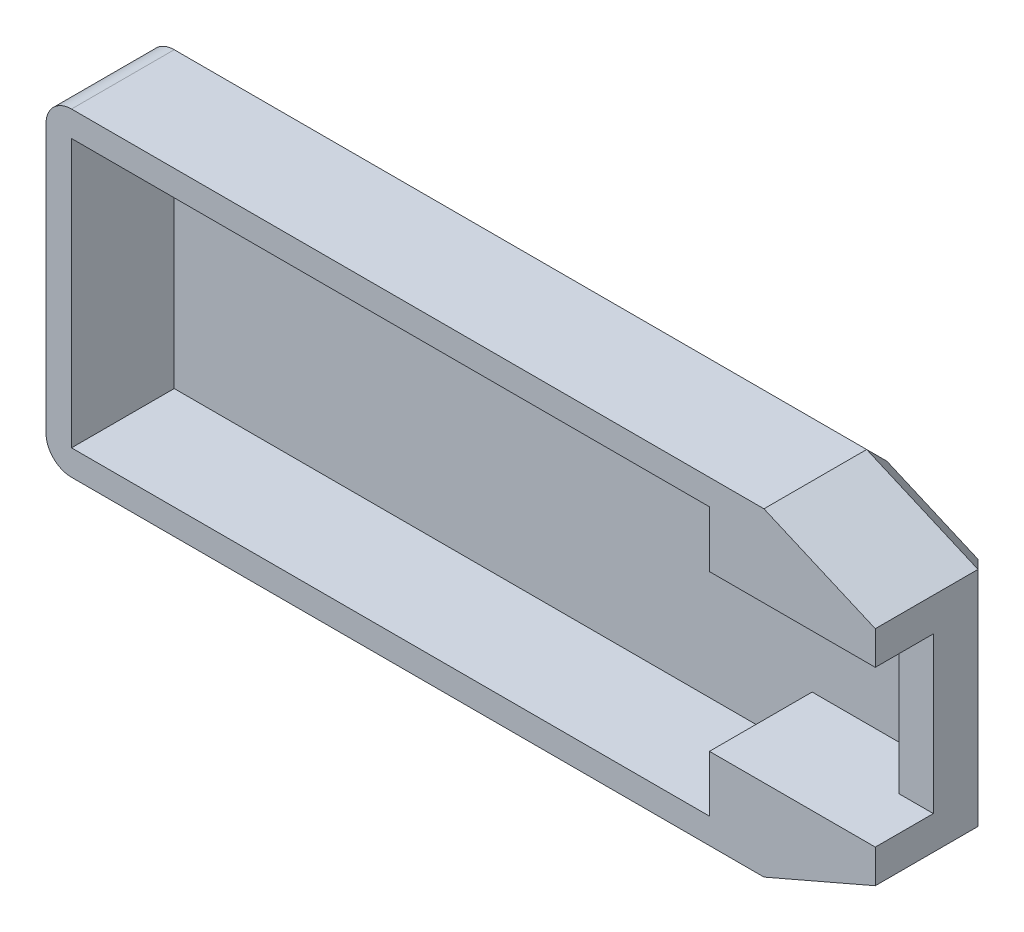
SolidWorks part; units mm, degrees
ref_plane "Спереди" through (0, 0, 0) normal (0, 0, 1) x (1, 0, 0)
ref_plane "Сверху" through (0, 0, 0) normal (0, 1, 0) x (1, 0, 0)
ref_plane "Справа" through (0, 0, 0) normal (1, 0, 0) x (0, 0, -1)
sketch "Эскиз1" plane through (0, 0, 0) normal (0, 0, 1) x (1, 0, 0)
  line L0 (-16.7031, 1.2008) -> (70.0547, 1.2008) construction
  line L1 (-16.7031, 11.7008) -> (33.2969, 11.7008) construction
  line L2 (-16.7031, 11.7008) -> (-16.7031, -9.2992) construction
  line L3 (-16.7031, -9.2992) -> (33.2969, -9.2992) construction
  line L4 (33.2969, 11.7008) -> (33.2969, -9.2992) construction
  line L5 (-16.7031, 11.7008) -> (33.2969, -9.2992) construction
  line L6 (-16.7031, -9.2992) -> (33.2969, 11.7008) construction
  line L7 (46.2969, 9.9258) -> (37.5703, 13.7008)
  line L8 (57.2969, 7.3008) -> (33.2969, 7.3008) construction
  line L9 (57.2969, 7.3008) -> (57.2969, -4.8992) construction
  line L10 (57.2969, -4.8992) -> (33.2969, -4.8992) construction
  line L11 (33.2969, 7.3008) -> (33.2969, -4.8992) construction
  line L12 (57.2969, 7.3008) -> (33.2969, -4.8992) construction
  line L13 (57.2969, -4.8992) -> (33.2969, 7.3008) construction
  line L14 (-18.7031, 13.7008) -> (37.5703, 13.7008)
  line L15 (-18.7031, 13.7008) -> (-18.7031, -11.2992)
  line L16 (-18.7031, -11.2992) -> (37.5703, -11.2992)
  line L17 (46.2969, 9.9258) -> (46.2969, -7.5242)
  line L20 (46.2969, -7.5242) -> (37.5703, -11.2992)
  point P4 (8.2969, 1.2008)
  point P7 (45.2969, 1.2008)
  point P12 (12.7969, 1.2008)
  dimension "D1" = 21
  dimension "D2" = 50
  dimension "D3" = 12.2
  dimension "D4" = 24
  dimension "D5" = 25
  dimension "D6" = 11
  dimension "D7" = 2
  dimension "D8" = 56.2734
extrude "Бобышка-Вытянуть1" add sketch "Эскиз1" along normal blind 2
sketch "Эскиз2" plane through (0, 0, 2) normal (0, 0, 1) x (1, 0, 0)
  line L0 (-18.7031, -11.2992) -> (37.5703, -11.2992) construction
  line L1 (-18.7031, 13.7008) -> (-18.7031, -11.2992) construction
  line L2 (46.2969, -7.5242) -> (46.2969, 9.9258) construction
  line L3 (37.5703, -11.2992) -> (46.2969, -7.5242) construction
  line L4 (-18.7031, -11.2992) -> (37.5703, -11.2992)
  line L5 (-18.7031, 13.7008) -> (-18.7031, -11.2992)
  line L6 (46.2969, -7.5242) -> (46.2969, 9.9258)
  line L7 (37.5703, -11.2992) -> (46.2969, -7.5242)
  line L8 (46.2969, 9.9258) -> (37.5703, 13.7008) construction
  line L9 (37.5703, 13.7008) -> (-18.7031, 13.7008) construction
  line L10 (46.2969, 9.9258) -> (37.5703, 13.7008)
  line L11 (37.5703, 13.7008) -> (-18.7031, 13.7008)
  line L12 (-16.7031, 1.2008) -> (49983.2969, 1.2008) construction
  line L13 (-16.7031, 11.7008) -> (33.2969, 11.7008)
  line L14 (-16.7031, 11.7008) -> (-16.7031, -9.2992)
  line L15 (-16.7031, -9.2992) -> (33.2969, -9.2992)
  line L16 (33.2969, 11.7008) -> (33.2969, 7.3008)
  line L17 (-16.7031, 11.7008) -> (33.2969, -9.2992) construction
  line L18 (-16.7031, -9.2992) -> (33.2969, 11.7008) construction
  line L19 (33.2969, -4.8992) -> (33.2969, -9.2992)
  line L20 (43.5969, -4.8992) -> (33.2969, -4.8992)
  line L21 (43.5969, -4.8992) -> (43.5969, 7.3008)
  line L22 (43.5969, 7.3008) -> (33.2969, 7.3008)
  line L24 (43.5969, -4.8992) -> (33.2969, 7.3008) construction
  line L25 (43.5969, 7.3008) -> (33.2969, -4.8992) construction
  point P10 (8.2969, 1.2008)
  point P13 (-16.7031, 1.2008)
  point P15 (38.4469, 1.2008)
  dimension "D1" = 2
  dimension "D2" = 2
  dimension "D3" = 2
  dimension "D4" = 50
  dimension "D5" = 12.2
  dimension "D6" = 10.3
extrude "Бобышка-Вытянуть2" add sketch "Эскиз2" along normal blind 3.5
sketch "Эскиз3" plane through (0, 0, 5.5) normal (0, 0, 1) x (1, 0, 0)
  line L0 (-18.7031, 13.7008) -> (-18.7031, -11.2992) construction
  line L1 (-16.7031, 11.7008) -> (-16.7031, -9.2992) construction
  line L2 (-16.7031, -9.2992) -> (33.2969, -9.2992) construction
  line L3 (33.2969, -9.2992) -> (33.2969, -4.8992) construction
  line L4 (33.2969, 7.3008) -> (33.2969, 11.7008) construction
  line L5 (43.5969, 7.3008) -> (33.2969, 7.3008) construction
  line L6 (33.2969, -4.8992) -> (43.5969, -4.8992) construction
  line L7 (-18.7031, -11.2992) -> (37.5703, -11.2992) construction
  line L8 (37.5703, -11.2992) -> (46.2969, -7.5242) construction
  line L10 (46.2969, -7.5242) -> (46.2969, 9.9258) construction
  line L11 (46.2969, 9.9258) -> (37.5703, 13.7008) construction
  line L12 (37.5703, 13.7008) -> (-18.7031, 13.7008) construction
  line L13 (33.2969, 11.7008) -> (-16.7031, 11.7008) construction
  line L14 (-18.7031, 13.7008) -> (-18.7031, -11.2992)
  line L15 (-16.7031, 11.7008) -> (-16.7031, -9.2992)
  line L16 (-16.7031, -9.2992) -> (33.2969, -9.2992)
  line L17 (33.2969, -9.2992) -> (33.2969, -4.8992)
  line L18 (33.2969, 7.3008) -> (33.2969, 11.7008)
  line L19 (46.2969, 7.3008) -> (33.2969, 7.3008)
  line L20 (33.2969, -4.8992) -> (46.2969, -4.8992)
  line L21 (-18.7031, -11.2992) -> (37.5703, -11.2992)
  line L22 (37.5703, -11.2992) -> (46.2969, -7.5242)
  line L24 (46.2969, -7.5242) -> (46.2969, -4.8992)
  line L25 (46.2969, 9.9258) -> (37.5703, 13.7008)
  line L26 (37.5703, 13.7008) -> (-18.7031, 13.7008)
  line L27 (33.2969, 11.7008) -> (-16.7031, 11.7008)
  line L28 (46.2969, 7.3008) -> (46.2969, 9.9258)
  point P4 (43.5969, 7.3008)
  point P10 (46.2969, 7.3008)
  point P12 (46.2969, -4.8992)
extrude "Бобышка-Вытянуть3" add sketch "Эскиз3" along normal blind 4.55
fillet "Скругление1" radius 2 2 edges at (-18.7031, -11.2992, 5.025) (-18.7031, 13.7008, 5.025)
chamfer "Фаска1" distance 2 angle 45 5 edges at (10.4336, 13.7008, 0) (-18.1173, 13.115, 0) (-18.7031, 1.2008, 0) (-18.1173, -10.7134, 0) (10.4336, -11.2992, 0)
chamfer "Фаска2" distance 2 angle 45 3 edges at (44.2453, 10.8133, 0) (46.2969, 1.2008, 0) (44.2453, -8.4117, 0)
